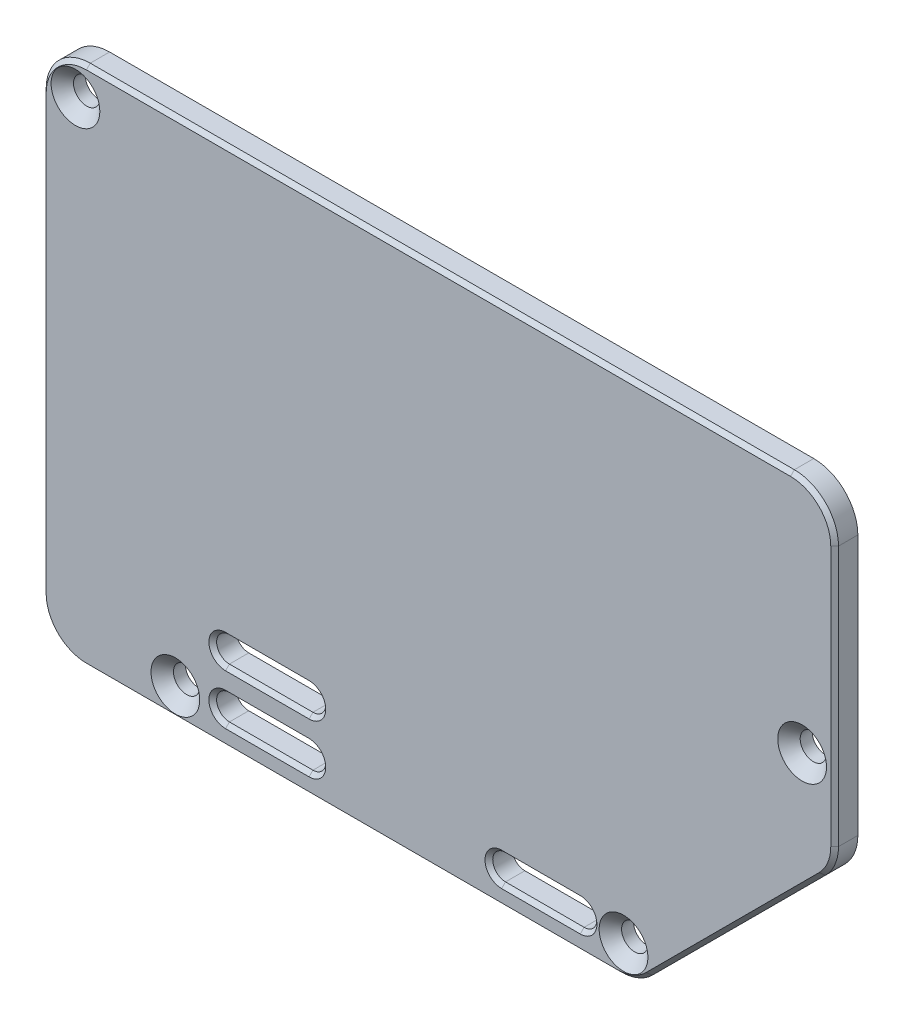
SolidWorks part; units mm, degrees
ref_plane "Front Plane" through (0, 0, 0) normal (0, 0, 1) x (1, 0, 0)
ref_plane "Top Plane" through (0, 0, 0) normal (0, 1, 0) x (1, 0, 0)
ref_plane "Right Plane" through (0, 0, 0) normal (1, 0, 0) x (0, 0, -1)
sketch "Sketch2" plane through (0, 0, 8.62) normal (0, 0, 1) x (1, 0, 0)
  line L0 (4.5, 66.2) -> (95.5, 66.2)
  line L1 (101.2, 60.5) -> (101.2, 26.864)
  line L2 (99.5305, 22.8335) -> (77.1665, 0.4695)
  line L3 (73.136, -1.2) -> (4.5, -1.2)
  line L4 (-1.2, 4.5) -> (-1.2, 60.5)
  line L5 (-1.5, 60.5) -> (-1.5, 4.5) construction
  arc A0 (4.5, -1.2) -> (-1.2, 4.5) centre (4.5, 4.5) cw
  arc A1 (77.1665, 0.4695) -> (73.136, -1.2) centre (73.136, 4.5) cw
  arc A2 (101.2, 26.864) -> (99.5305, 22.8335) centre (95.5, 26.864) cw
  arc A3 (95.5, 66.2) -> (101.2, 60.5) centre (95.5, 60.5) cw
  arc A4 (4.5, 66.2) -> (-1.2, 60.5) centre (4.5, 60.5) ccw
  arc A5 (-1.5, 4.5) -> (4.5, -1.5) centre (4.5, 4.5) ccw construction
  arc A6 (4.5, 66.5) -> (-1.5, 60.5) centre (4.5, 60.5) ccw construction
  arc A7 (101.5, 60.5) -> (95.5, 66.5) centre (95.5, 60.5) ccw construction
  arc A8 (73.136, -1.5) -> (77.3787, 0.2574) centre (73.136, 4.5) ccw construction
  circle A9 centre (3.0858, 61.9142) radius 1.5 construction
  circle A10 centre (16, 2.5) radius 1.5 construction
  circle A11 centre (73.9175, 2.659) radius 1.5 construction
  circle A12 centre (97, 35.5) radius 1.5 construction
  arc A14 (101.3205, 25.4074) -> (101.5, 26.864) centre (95.5, 26.864) ccw construction
  dimension "D1" = 0.3
  dimension "D2" = 3
extrude "Boss-Extrude1" add sketch "Sketch2" along normal blind 3
hole_wizard "CSK for M3 Flat Head Machine Screw1" positions "Sketch4" profile "Sketch5" countersink size "M3" standard "ANSI Metric" end condition through all
sketch "Sketch4" plane through (0, 0, 11.62) normal (0, 0, 1) x (1, 0, 0)
  point P0 (3.0858, 61.9142)
  point P3 (16, 2.5)
  point P6 (73.9175, 2.659)
  point P9 (97, 35.5)
sketch "Sketch5" plane through (3.0858, 61.9142, 11.62) normal (1, 0, 0) x (0, -1, 0)
  line L0 (0, 0) -> (0, 3)
  line L1 (0, 3) -> (1.7, 3)
  line L2 (1.7, 3) -> (1.7, 1.45)
  line L3 (1.7, 1.45) -> (3.15, 0)
  line L5 (3.15, 0) -> (0, 0)
  line L6 (-1.7, 1.45) -> (-3.15, 0) construction
  line L11 (0, -6.35) -> (0, 107.95) construction
  dimension "Thru Hole Dia." = 3.4
  dimension "Thru Hole Depth" = 3
  dimension "Near C'Sink Dia." = 6.3
  dimension "Near C'Sink Angle" = 90
sketch "Sketch6" plane through (0, 0, 11.62) normal (0, 0, 1) x (1, 0, 0)
  line L0 (33.278, 9.5885) -> (22.483, 9.5885) construction
  line L1 (33.278, 7.9375) -> (22.483, 7.9375)
  line L2 (33.278, 11.2395) -> (22.483, 11.2395)
  line L3 (33.278, 3.1115) -> (22.483, 3.1115) construction
  line L4 (33.278, 1.4605) -> (22.483, 1.4605)
  line L5 (33.278, 4.7625) -> (22.483, 4.7625)
  line L6 (27.8805, 11.85) -> (27.8805, 9.5885) construction
  line L8 (34.3805, 11.85) -> (21.3805, 11.85) construction
  line L10 (68.326, 3.048) -> (58.166, 3.048) construction
  line L11 (68.326, 1.397) -> (58.166, 1.397)
  line L12 (68.326, 4.699) -> (58.166, 4.699)
  line L13 (27.8805, 3.1115) -> (27.8805, 0.85) construction
  line L14 (21.3805, 0.85) -> (34.3805, 0.85) construction
  arc A0 (33.278, 7.9375) -> (33.278, 11.2395) centre (33.278, 9.5885) ccw
  arc A1 (22.483, 11.2395) -> (22.483, 7.9375) centre (22.483, 9.5885) ccw
  arc A2 (33.278, 1.4605) -> (33.278, 4.7625) centre (33.278, 3.1115) ccw
  arc A3 (22.483, 4.7625) -> (22.483, 1.4605) centre (22.483, 3.1115) ccw
  arc A4 (68.326, 1.397) -> (68.326, 4.699) centre (68.326, 3.048) ccw
  arc A5 (58.166, 4.699) -> (58.166, 1.397) centre (58.166, 3.048) ccw
  point P2 (27.8805, 9.5885)
  point P7 (27.8805, 3.1115)
  point P26 (63.246, 3.048)
  dimension "D1" = 3.302
  dimension "D2" = 3.175
  dimension "D3" = 10.795
  dimension "D4" = 3.302
extrude "Cut-Extrude1" cut sketch "Sketch6" against normal through all
sketch "Sketch7" plane through (0, 0, 11.62) normal (0, 0, 1) x (1, 0, 0)
  line L1 (13.5247, 51.635) -> (61.5247, 51.635)
  line L2 (12.8897, 51) -> (12.8897, 14.6)
  line L3 (13.5247, 13.965) -> (61.5247, 13.965)
  line L4 (62.1597, 51) -> (62.1597, 14.6)
  arc A4 (61.5247, 51.635) -> (62.1597, 51) centre (61.5247, 51) cw
  arc A5 (61.5247, 13.965) -> (62.1597, 14.6) centre (61.5247, 14.6) ccw
  arc A6 (12.8897, 14.6) -> (13.5247, 13.965) centre (13.5247, 14.6) ccw
  arc A7 (13.5247, 51.635) -> (12.8897, 51) centre (13.5247, 51) ccw
  dimension "D2" = 0.635
split line "Split Line1" [suppressed]
chamfer "Chamfer1" distance 0.5 angle 45 22 edges at (63.246, 1.397, 11.62) (69.977, 3.048, 11.62) (56.515, 3.048, 11.62) (63.246, 4.699, 11.62) (27.8805, 1.4605, 11.62) (34.929, 3.1115, 11.62) (20.832, 3.1115, 11.62) (27.8805, 4.7625, 11.62) (27.8805, 7.9375, 11.62) (34.929, 9.5885, 11.62) (20.832, 9.5885, 11.62) (27.8805, 11.2395, 11.62) (100.7661, 24.6827, 11.62) (101.2, 43.682, 11.62) (88.3485, 11.6515, 11.62) (99.5305, 64.5305, 11.62) (75.3173, -0.7661, 11.62) (50, 66.2, 11.62) (38.818, -1.2, 11.62) (0.4695, 64.5305, 11.62) (0.4695, 0.4695, 11.62) (-1.2, 32.5, 11.62)
